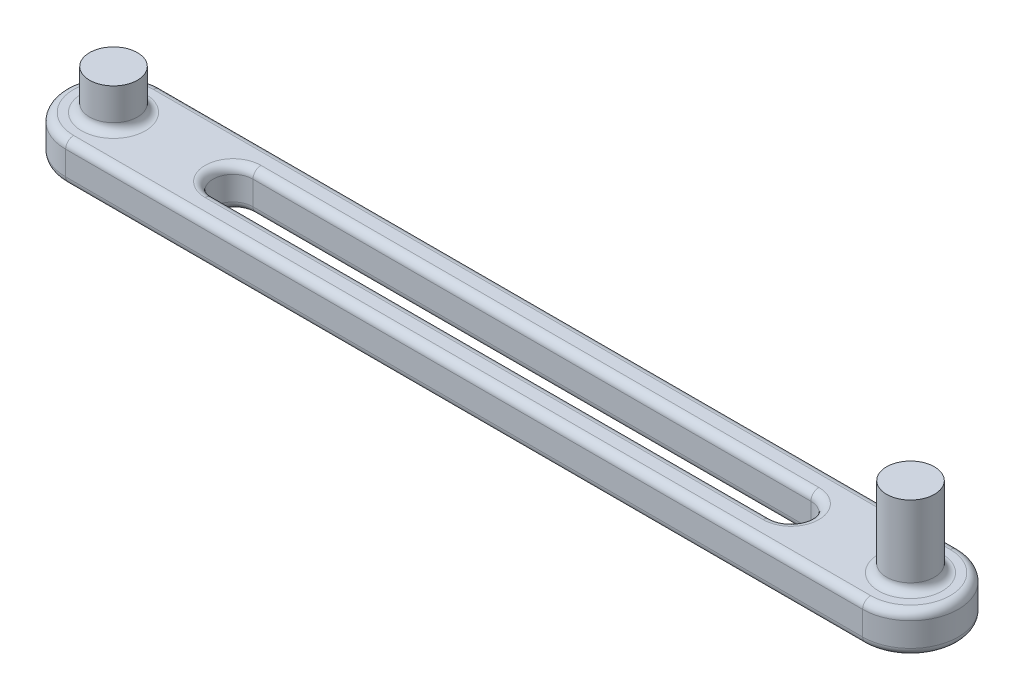
SolidWorks part; units mm, degrees
ref_plane "Front" through (0, 0, 0) normal (0, 0, 1) x (1, 0, 0)
ref_plane "Top" through (0, 0, 0) normal (0, 1, 0) x (1, 0, 0)
ref_plane "Right" through (0, 0, 0) normal (1, 0, 0) x (0, 0, -1)
sketch "草图1" plane through (0, 0, 0) normal (0, 1, 0) x (1, 0, 0)
  line L0 (-59.0043, 0) -> (63.069, 0) construction
  circle A0 centre (-50, 0) radius 6
  circle A1 centre (50, 0) radius 6
  dimension "D1" = 12
  dimension "D3" = 12
  dimension "D2" = 100
  dimension "D4" = 50
extrude "凸台-拉伸1" add sketch "草图1" along normal blind 5
sketch "草图3" plane through (0, 0, 0) normal (0, 1, 0) x (1, 0, 0)
  line L0 (-61.778, 0) -> (78.4405, 0) construction
  line L1 (0, 36.4306) -> (0, -33.6787) construction
  line L6 (-50, 6) -> (50, 6)
  line L7 (50, 6) -> (50, -6)
  line L8 (50, -6) -> (-50, -6)
  line L9 (-50, -6) -> (-50, 6)
  circle A2 centre (-50, 0) radius 6 construction
  circle A3 centre (50, 0) radius 6 construction
extrude "凸台-拉伸3" add sketch "草图3" along normal blind 5
sketch "草图4" plane through (0, 5, 0) normal (0, 1, 0) x (1, 0, 0)
  circle A0 centre (-50, 0) radius 3
  dimension "D1" = 6
sketch "草图5" plane through (0, 5, 0) normal (0, 1, 0) x (1, 0, 0)
  circle A0 centre (50, 0) radius 3
  dimension "D1" = 6
sketch "草图6" plane through (0, 5, 0) normal (0, 1, 0) x (1, 0, 0)
  line L0 (-65.6937, 0) -> (69.5957, 0) construction
  circle A2 centre (-35, 0) radius 2.5
  circle A3 centre (35, 0) radius 2.5
  dimension "D3" = 5
  dimension "D4" = 5
  dimension "D1" = 35
  dimension "D2" = 35
extrude "切除-拉伸3" cut sketch "草图6" against normal through all
sketch "草图7" plane through (0, 5, 0) normal (0, 1, 0) x (1, 0, 0)
  line L4 (-35, 2.5) -> (35, 2.5)
  line L5 (35, 2.5) -> (35, -2.5)
  line L6 (35, -2.5) -> (-35, -2.5)
  line L7 (-35, -2.5) -> (-35, 2.5)
  circle A2 centre (-35, 0) radius 2.5 construction
  circle A3 centre (35, 0) radius 2.5 construction
extrude "切除-拉伸4" cut sketch "草图7" against normal through all
extrude "凸台-拉伸4" add sketch "草图4" along normal blind 5
extrude "凸台-拉伸5" add sketch "草图5" along normal blind 10
fillet "圆角1" radius 1 2 edges at (-50, 5, 3) (50, 5, 3)
fillet "圆角2" radius 1 16 edges at (-56, 0, 0) (0, 0, 6) (0, 5, 6) (56, 0, 0) (0, 0, -6) (0, 5, -6) (0, 0, 2.5) (-37.5, 0, 0) (0, 0, -2.5) (37.5, 0, 0) (-56, 5, 0) (56, 5, 0) (-37.5, 5, 0) (0, 5, 2.5) (37.5, 5, 0) (0, 5, -2.5)
